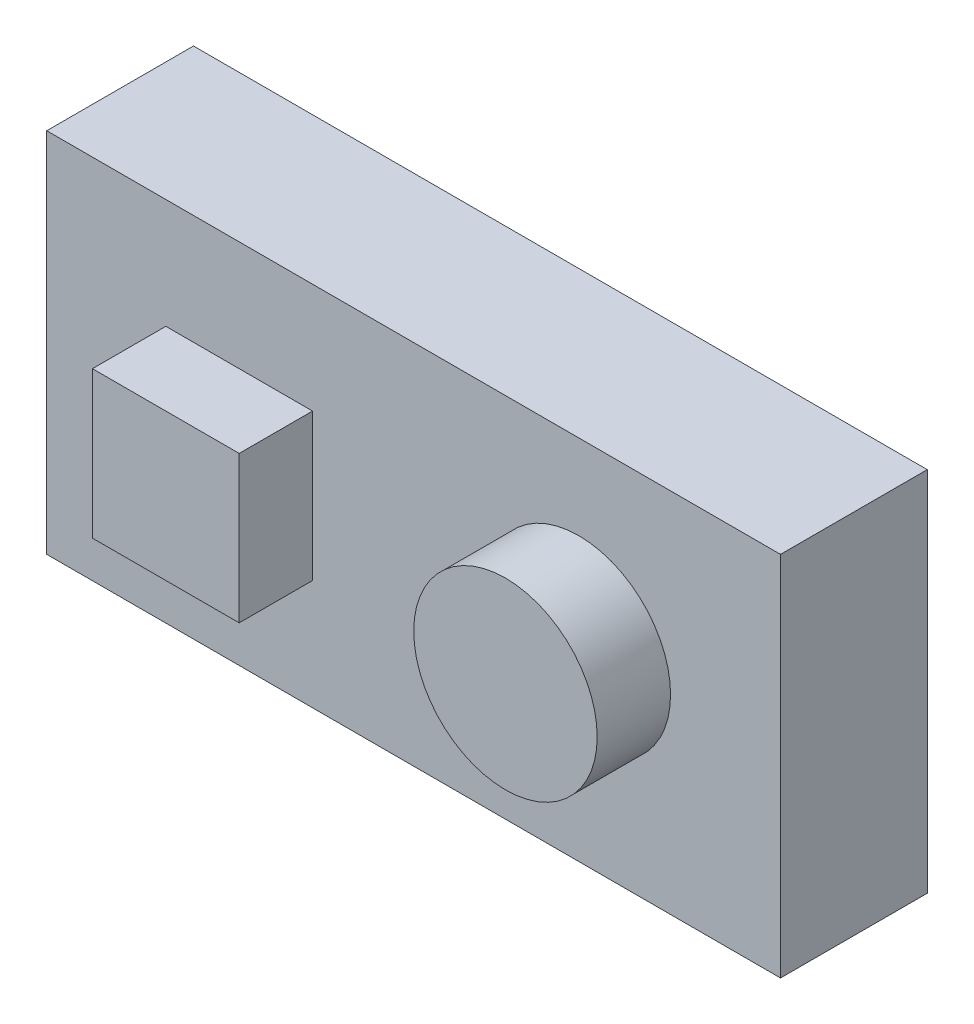
SolidWorks part; units mm, degrees
ref_plane "Front Plane" through (0, 0, 0) normal (0, 0, 1) x (1, 0, 0)
ref_plane "Top Plane" through (0, 0, 0) normal (0, 1, 0) x (1, 0, 0)
ref_plane "Right Plane" through (0, 0, 0) normal (1, 0, 0) x (0, 0, -1)
sketch "Sketch1" plane through (0, 0, 0) normal (0, 0, 1) x (1, 0, 0)
  line L1 (0, 0) -> (100, 0)
  line L2 (0, 0) -> (0, 50)
  line L3 (0, 50) -> (100, 50)
  line L4 (100, 0) -> (100, 50)
  dimension "D1" = 100
  dimension "D2" = 50
extrude "Boss-Extrude1" add sketch "Sketch1" along normal blind 20
sketch "Sketch2" plane through (0, 0, 20) normal (0, 0, 1) x (1, 0, 0)
  line L1 (16.2262, 35.0287) -> (36.2262, 35.0287)
  line L2 (16.2262, 35.0287) -> (16.2262, 15.0287)
  line L3 (16.2262, 15.0287) -> (36.2262, 15.0287)
  line L4 (36.2262, 35.0287) -> (36.2262, 15.0287)
  circle A0 centre (72.5159, 25.965) radius 12.5
  point P6 (36.4905, 15.672)
  point P7 (16.2262, 15.0287)
  dimension "D3" = 25
  dimension "D1" = 20
  dimension "D2" = 20
extrude "Boss-Extrude2" add sketch "Sketch2" along normal blind 10
